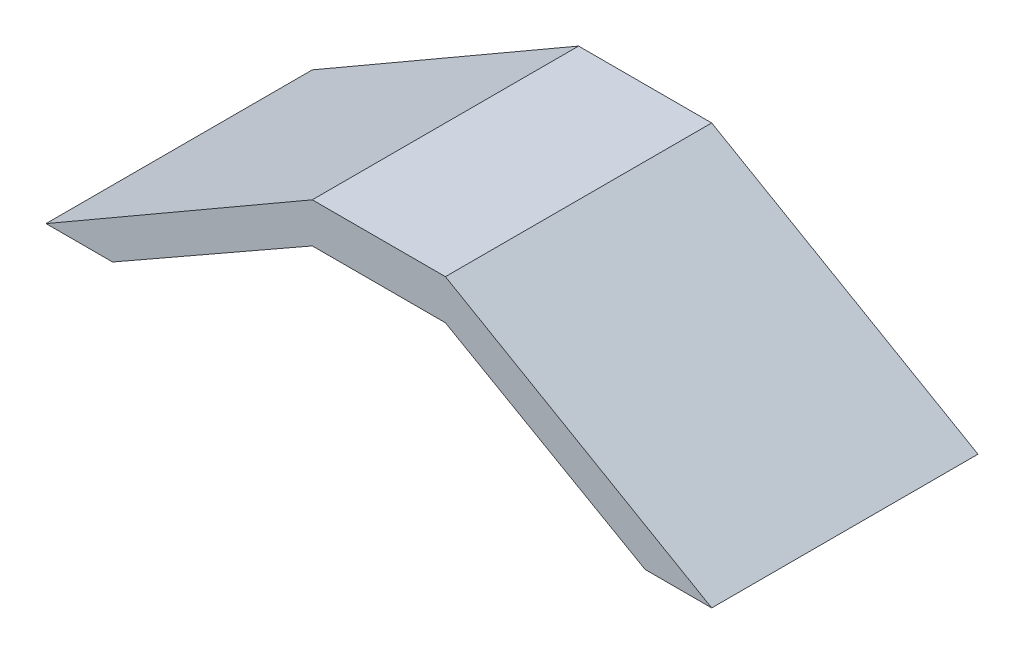
SolidWorks part; units mm, degrees
ref_plane "Front Plane" through (0, 0, 0) normal (0, 0, 1) x (1, 0, 0)
ref_plane "Top Plane" through (0, 0, 0) normal (0, 1, 0) x (1, 0, 0)
ref_plane "Right Plane" through (0, 0, 0) normal (1, 0, 0) x (0, 0, -1)
sketch "Sketch1" plane through (0, 0, 0) normal (0, 0, 1) x (1, 0, 0)
  line L0 (0, 0) -> (2000, 0)
  line L1 (2000, 0) -> (0, 1154.7005)
  line L2 (0, 1154.7005) -> (0, 0)
  line L3 (-500, 1154.7005) -> (-500, 0) construction
  line L4 (0, 0) -> (-1000, 0)
  line L5 (0, 0) -> (0, 1154.7005)
  line L6 (0, 1154.7005) -> (-1000, 1154.7005)
  line L7 (-1000, 0) -> (-1000, 1154.7005)
  line L8 (-1000, 0) -> (-3000, 0)
  line L9 (-3000, 0) -> (-1000, 1154.7005)
  line L10 (-1000, 1154.7005) -> (-1000, 0)
  line L11 (-2000, 0) -> (-1000, 577.3503)
  line L12 (-1000, 577.3503) -> (0, 577.3503)
  line L13 (0, 577.3503) -> (1000, 0)
  line L14 (-2500, 0) -> (-1000, 854.7005)
  line L15 (-1000, 854.7005) -> (0, 854.7005)
  line L16 (0, 854.7005) -> (1500, 0)
  dimension "D1" = 2000
  dimension "D2" = 30
  dimension "D3" = 1000
  dimension "D4" = 500
  dimension "D5" = 300
  dimension "D6" = 500
extrude "Boss-Extrude1" add sketch "Sketch1" against normal blind 2000 contours L8 L14 L7 L9 | L3 L6 L7 L15 | L6 L3 L15 L2 | L2 L16 L0 L1
